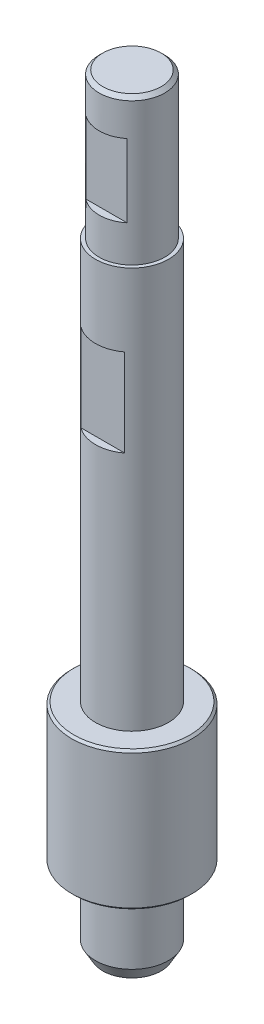
SolidWorks part; units mm, degrees
material "1.0501 (C35)"
ref_plane "Plan de face" through (0, 0, 0) normal (0, 0, 1) x (1, 0, 0)
ref_plane "Plan de dessus" through (0, 0, 0) normal (0, 1, 0) x (1, 0, 0)
ref_plane "Plan de droite" through (0, 0, 0) normal (1, 0, 0) x (0, 0, -1)
sketch "Esquisse1" plane through (0, 0, 0) normal (0, 0, 1) x (1, 0, 0)
  line L0 (5, 73.5571) -> (5, -1.4429)
  line L1 (5, -1.4429) -> (8.25, -1.4429)
  line L2 (8.25, -1.4429) -> (8.25, -20.4429)
  line L3 (8.25, -20.4429) -> (5, -20.4429)
  line L4 (5, -20.4429) -> (5, -31.4429)
  line L5 (5, -31.4429) -> (0, -31.4429)
  line L6 (5, 73.5571) -> (0, 73.5571)
  line L7 (0, 73.5571) -> (0, -31.4429)
  dimension "D1" = 5
  dimension "D2" = 5
  dimension "D3" = 8.25
  dimension "D4" = 11
  dimension "D5" = 19
  dimension "D6" = 75
revolve "Révolution1" add sketch "Esquisse1" angle 360 about L7
chamfer "Chanfrein1" distance 1 angle 60 1 edges at (-5, -31.4429, 0)
ref_plane "Plan1" through (0, 0, 5) normal (0, 0, 1) x (1, 0, 0)
sketch "Esquisse3" plane through (0, 0, 5) normal (0, 0, 1) x (1, 0, 0)
  line L0 (5, 73.5571) -> (-5, 73.5571) construction
  line L1 (-24.2665, 43.5571) -> (24.2665, 43.5571)
  line L2 (-24.2665, 43.5571) -> (-24.2665, 31.5571)
  line L3 (-24.2665, 31.5571) -> (24.2665, 31.5571)
  line L4 (24.2665, 43.5571) -> (24.2665, 31.5571)
  line L5 (-24.2665, 43.5571) -> (24.2665, 31.5571) construction
  line L6 (-24.2665, 31.5571) -> (24.2665, 43.5571) construction
  point P0 (0, 37.5571)
  dimension "D1" = 36
  dimension "D2" = 12
extrude "Enlèv. mat.-Extru.1" cut sketch "Esquisse3" against normal blind 1
sketch "Esquisse4" plane through (0, 73.5571, 0) normal (0, 1, 0) x (1, 0, 0)
  circle A0 centre (0, 0) radius 4.5
extrude "Enlèv. mat.-Extru.2" cut sketch "Esquisse4" against normal blind 20 flip side to cut
sketch "Esquisse5" plane through (0, 0, 5) normal (0, 0, 1) x (1, 0, 0)
  line L0 (4.5, 73.5571) -> (-4.5, 73.5571) construction
  line L1 (-18.683, 68.5571) -> (18.683, 68.5571)
  line L2 (-18.683, 68.5571) -> (-18.683, 58.5571)
  line L3 (-18.683, 58.5571) -> (18.683, 58.5571)
  line L4 (18.683, 68.5571) -> (18.683, 58.5571)
  line L5 (-18.683, 68.5571) -> (18.683, 58.5571) construction
  line L6 (-18.683, 58.5571) -> (18.683, 68.5571) construction
  point P0 (0, 63.5571)
  dimension "D1" = 10
  dimension "D2" = 10
extrude "Enlèv. mat.-Extru.3" cut sketch "Esquisse5" against normal blind 1.5
chamfer "Chanfrein2" distance 0.5 angle 45 1 edges at (-4.5, 73.5571, 0)
chamfer "Chanfrein3" distance 0.3 angle 45 2 edges at (-8.25, -1.4429, 0) (-8.25, -20.4429, 0)
